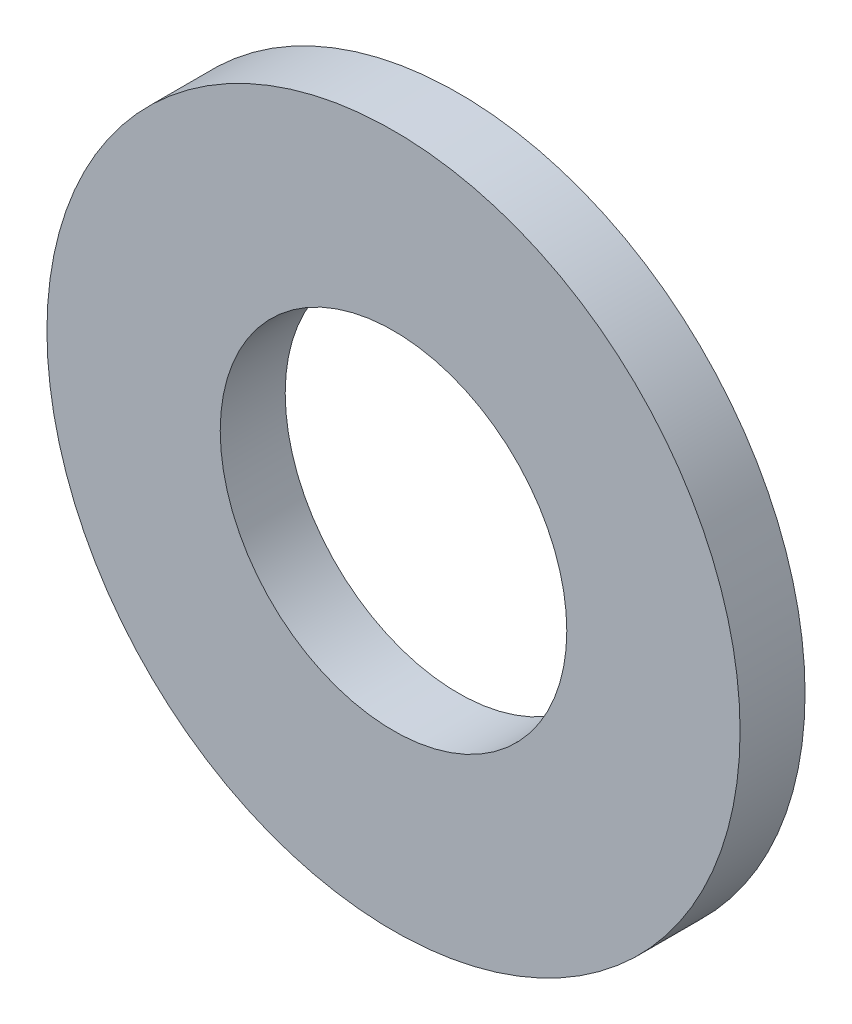
SolidWorks part; units mm, degrees
ref_plane "前视基准面" through (0, 0, 0) normal (0, 0, 1) x (1, 0, 0)
ref_plane "上视基准面" through (0, 0, 0) normal (0, 1, 0) x (1, 0, 0)
ref_plane "右视基准面" through (0, 0, 0) normal (1, 0, 0) x (0, 0, -1)
sketch "草图1" plane through (0, 0, 0) normal (0, 0, 1) x (1, 0, 0)
  circle A0 centre (0, 0) radius 4
  circle A1 centre (0, 0) radius 8
  dimension "D1" = 16
  dimension "D2" = 8
extrude "凸台-拉伸1" add sketch "草图1" along normal blind 1.5
